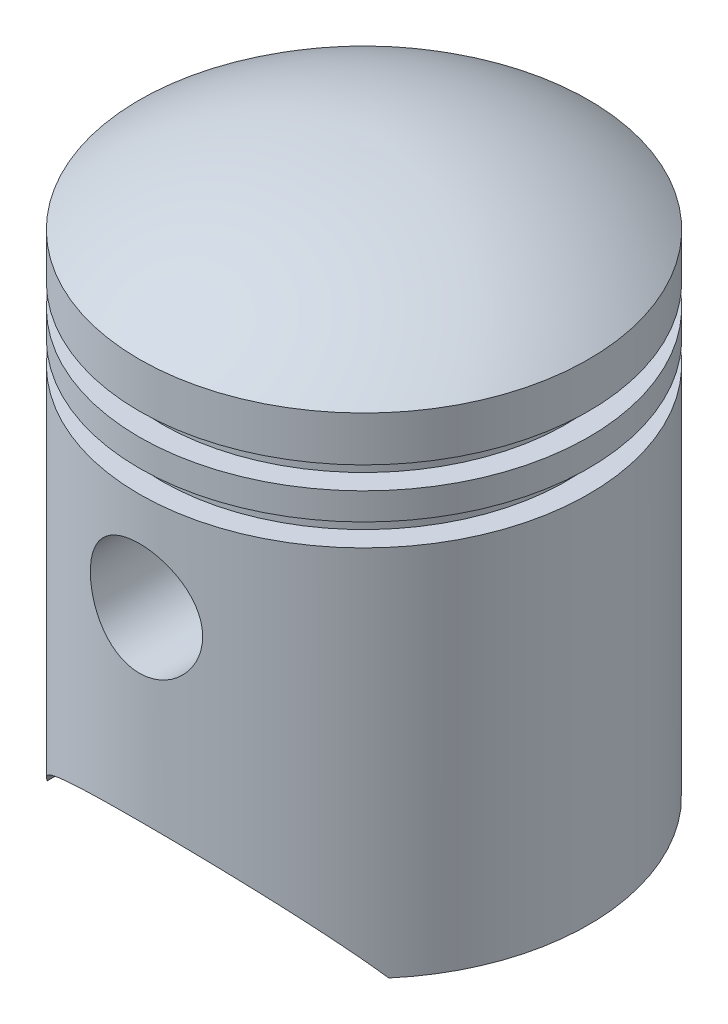
SolidWorks part; units mm, degrees
ref_plane "Front Plane" through (0, 0, 0) normal (0, 0, 1) x (1, 0, 0)
ref_plane "Top Plane" through (0, 0, 0) normal (0, 1, 0) x (1, 0, 0)
ref_plane "Right Plane" through (0, 0, 0) normal (1, 0, 0) x (0, 0, -1)
sketch "Sketch1" plane through (0, 0, 0) normal (0, 0, 1) x (1, 0, 0)
  line L0 (635, 0) -> (635, 1054.1)
  line L1 (635, 1257.3) -> (571.5, 1257.3)
  line L2 (571.5, 1257.3) -> (571.5, 1193.8)
  line L3 (571.5, 1193.8) -> (635, 1193.8)
  line L4 (635, 1117.6) -> (571.5, 1117.6)
  line L5 (571.5, 1117.6) -> (571.5, 1054.1)
  line L6 (571.5, 1054.1) -> (635, 1054.1)
  line L7 (635, 1257.3) -> (635, 1384.3)
  line L8 (635, 1117.6) -> (635, 1193.8)
  line L9 (584.2, 0) -> (584.2, 1003.3)
  line L10 (520.7, 1003.3) -> (584.2, 1003.3)
  line L11 (520.7, 1155.7) -> (520.7, 1003.3)
  line L12 (520.7, 1155.7) -> (520.7, 1155.7)
  line L13 (520.7, 1155.7) -> (520.7, 1155.7)
  line L14 (520.7, 1155.7) -> (520.7, 1155.7)
  line L15 (520.7, 1308.1) -> (520.7, 1155.7)
  line L16 (584.2, 1308.1) -> (520.7, 1308.1)
  line L17 (584.2, 1308.1) -> (584.2, 1358.5066)
  line L18 (635, 0) -> (584.2, 0)
  line L20 (0, 1587.5) -> (0, 1536.6838)
  arc A0 (635, 1384.3) -> (0, 1587.5) centre (24.9904, 571.8074) ccw
  arc A1 (584.2, 1358.5066) -> (0, 1536.6838) centre (24.9904, 571.8074) ccw
  arc A2 (584.2, 1358.5066) -> (1.2495, 1536.7154) centre (24.9904, 571.8074) ccw construction
  dimension "D4" = 1016
  dimension "D1" = 635
  dimension "D2" = 1587.5
  dimension "D3" = 1384.3
  dimension "D5" = 127
  dimension "D6" = 63.5
  dimension "D7" = 63.5
  dimension "D8" = 76.2
  dimension "D9" = 63.5
  dimension "D10" = 50.8
revolve "Revolve1" add sketch "Sketch1" angle 360 about L20
sketch "Sketch2" plane through (0, 0, 0) normal (0, 0, 1) x (1, 0, 0)
  line L0 (-635, 0) -> (635, 0) construction
  line L1 (0, 774.7) -> (0, 1587.5) construction
  line L2 (-482.6, 0) -> (482.6, 0)
  circle A0 centre (0, 774.7) radius 158.75
  arc A1 (-482.6, 0) -> (482.6, 0) centre (0, -331.47) cw
  point P5 (0, 254)
  dimension "D1" = 317.5
  dimension "D2" = 812.8
  dimension "D3" = 965.2
  dimension "D4" = 254
extrude "Cut-Extrude1" cut sketch "Sketch2" against normal through all both and the other way through all
sketch "Sketch3" plane through (0, 0, 0) normal (0, 0, 1) x (1, 0, 0)
  circle A0 centre (0, 774.7) radius 184.15
  circle A1 centre (0, 774.7) radius 158.75
  dimension "D1" = 368.3
  dimension "D2" = 317.5
extrude "Boss-Extrude1" add sketch "Sketch3" along normal up to surface (302.9119 mm away) from offset 304.8
mirror "Mirror1" about plane through (0, 0, 0) normal (0, 0, 1) of "Boss-Extrude1"
